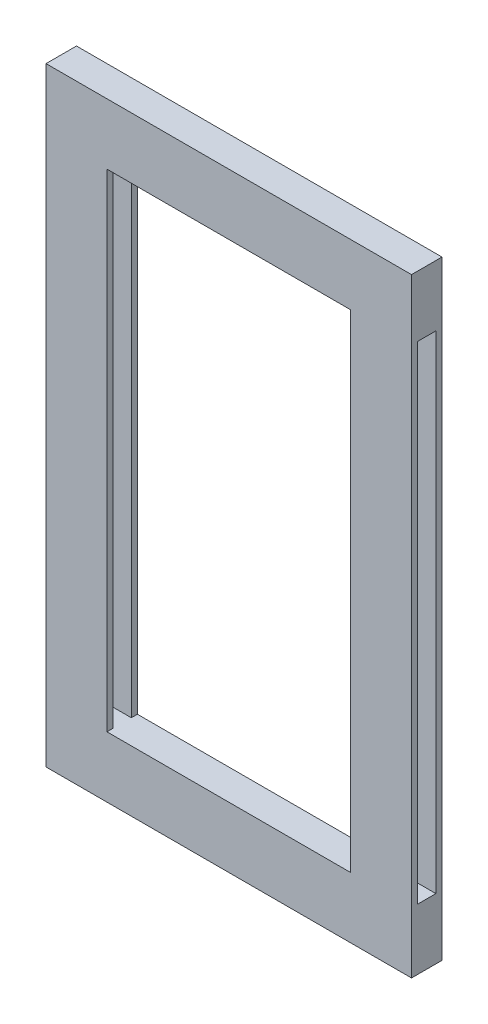
SolidWorks part; units mm, degrees
ref_plane "Alzado" through (0, 0, 0) normal (0, 0, 1) x (1, 0, 0)
ref_plane "Planta" through (0, 0, 0) normal (0, 1, 0) x (1, 0, 0)
ref_plane "Vista lateral" through (0, 0, 0) normal (1, 0, 0) x (0, 0, -1)
sketch "Croquis1" plane through (0, 0, 0) normal (0, 0, 1) x (1, 0, 0)
  line L1 (0, 0) -> (-60, 0)
  line L2 (0, 0) -> (0, 100)
  line L3 (0, 100) -> (-60, 100)
  line L4 (-60, 0) -> (-60, 100)
  dimension "D1" = 60
  dimension "D2" = 100
extrude "Saliente-Extruir1" add sketch "Croquis1" along normal blind 5
sketch "Croquis3" plane through (-60, 0, 0) normal (-1, 0, 0) x (0, 0, 1)
  line L0 (5, 100) -> (5, 0) construction
  line L1 (1, 10) -> (4, 10)
  line L2 (1, 10) -> (1, 90)
  line L3 (1, 90) -> (4, 90)
  line L4 (4, 10) -> (4, 90)
  line L5 (1, 10) -> (4, 90) construction
  line L6 (1, 90) -> (4, 10) construction
  line L7 (5, 100) -> (0, 100) construction
  point P0 (2.5, 50)
  dimension "D1" = 80
  dimension "D2" = 3
  dimension "D3" = 1
  dimension "D4" = 10
extrude "Cortar-Extruir2" cut sketch "Croquis3" against normal up to vertex (60 mm away)
sketch "Croquis4" plane through (0, 0, 0) normal (0, 0, -1) x (-1, 0, 0)
  line L0 (0, 100) -> (60, 100) construction
  line L1 (50, 10) -> (10, 10)
  line L2 (50, 10) -> (50, 90)
  line L3 (50, 90) -> (10, 90)
  line L4 (10, 10) -> (10, 90)
  line L5 (50, 10) -> (10, 90) construction
  line L6 (50, 90) -> (10, 10) construction
  line L7 (60, 100) -> (60, 0) construction
  point P0 (30, 50)
  dimension "D1" = 10
  dimension "D2" = 80
  dimension "D3" = 10
  dimension "D4" = 40
extrude "Cortar-Extruir3" cut sketch "Croquis4" against normal blind 28
